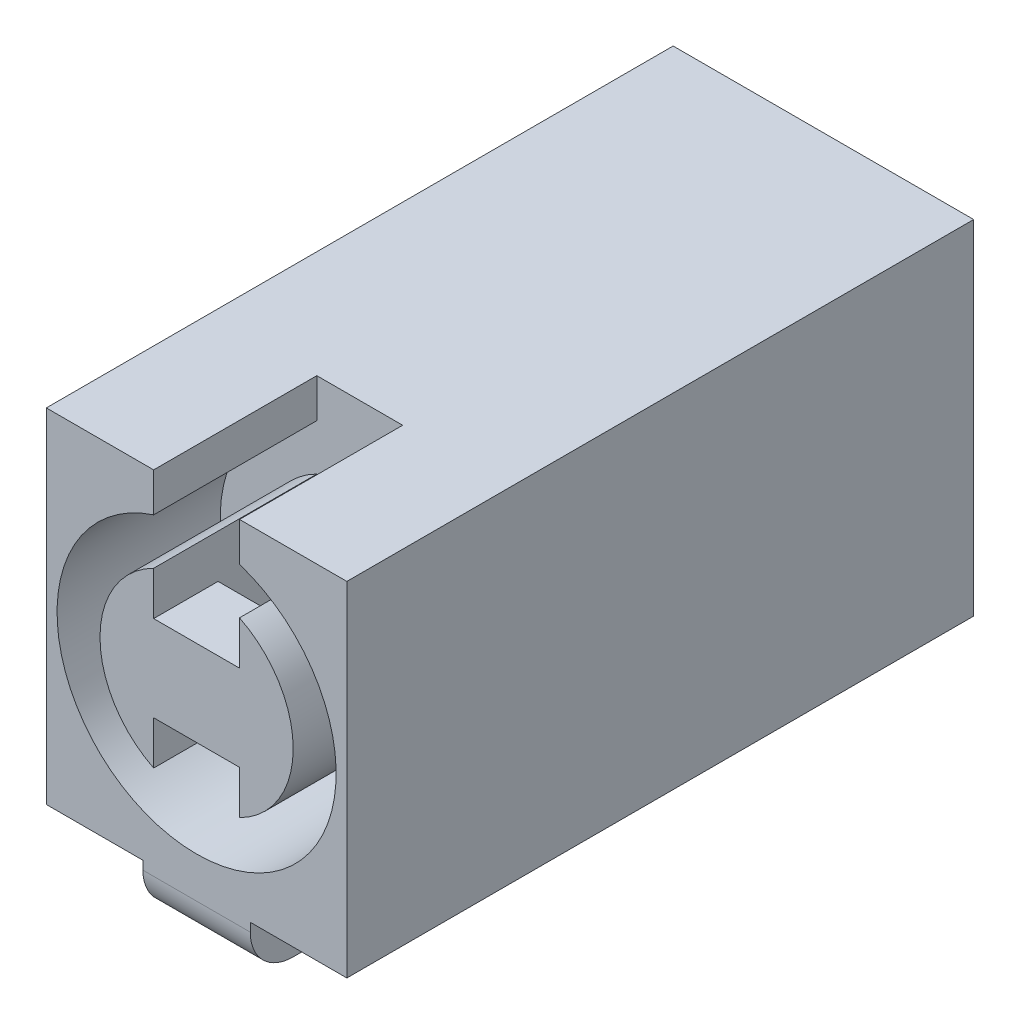
SolidWorks part; units mm, degrees
material "ABS"
ref_plane "Płaszczyzna przednia" through (0, 0, 0) normal (0, 0, 1) x (1, 0, 0)
ref_plane "Płaszczyzna górna" through (0, 0, 0) normal (0, 1, 0) x (1, 0, 0)
ref_plane "Płaszczyzna prawa" through (0, 0, 0) normal (1, 0, 0) x (0, 0, -1)
sketch "Szkic1" plane through (0, 0, 0) normal (0, 1, 0) x (1, 0, 0)
  line L1 (0, 0) -> (7, 0)
  line L2 (0, 0) -> (0, 14.6)
  line L3 (0, 14.6) -> (7, 14.6)
  line L4 (7, 0) -> (7, 14.6)
  dimension "D1" = 7
  dimension "D2" = 14.6
extrude "Dodanie-wyciągnięcie1" add sketch "Szkic1" along normal blind 8
sketch "Szkic2" plane through (0, 0, 0) normal (0, -1, 0) x (1, 0, 0)
  line L0 (7, 0) -> (7, -14.6) construction
  line L1 (2.5, -9.8) -> (4.5, -9.8)
  line L2 (2.5, -9.8) -> (2.5, -4.8)
  line L3 (2.5, -4.8) -> (4.5, -4.8)
  line L4 (4.5, -9.8) -> (4.5, -4.8)
  line L5 (0, 0) -> (7, 0) construction
  point P6 (7, -7.3)
  point P7 (4.5, -7.3)
  point P10 (3.5, 0)
  point P11 (3.5, -4.8)
  dimension "D1" = 5
  dimension "D2" = 2
extrude "Wytnij-wyciągnięcie1" cut sketch "Szkic2" against normal blind 3.5
sketch "Szkic7" plane through (0, 0, 0) normal (0, 0, 1) x (1, 0, 0)
  line L0 (0, 8) -> (7, 8) construction
  line L3 (0, 8) -> (0, 0) construction
  circle A0 centre (3.5, 4) radius 3.25
  circle A1 centre (3.5, 4) radius 2.25
  point P5 (3.5, 8)
  point P7 (0, 4)
  dimension "D1" = 1
  dimension "D2" = 6.5
extrude "Wytnij-wyciągnięcie4" cut sketch "Szkic7" against normal blind 3.8 contours A0 A1
sketch "Szkic10" plane through (0, 0, 0) normal (0, 0, 1) x (1, 0, 0)
  line L0 (0, 8) -> (7, 8) construction
  line L19 (4.5, 7.0923) -> (2.5, 7.0923)
  line L20 (4.5, 7.0923) -> (4.5, 0.9077)
  line L21 (4.5, 0.9077) -> (2.5, 0.9077)
  line L22 (2.5, 7.0923) -> (2.5, 0.9077)
  circle A2 centre (3.5, 4) radius 3.25 construction
  point P6 (3.5, 8)
  point P13 (3.5, 7.0923)
  dimension "D1" = 2
extrude "Wytnij-wyciągnięcie6" cut sketch "Szkic10" against normal blind 3.8
sketch "Szkic12" plane through (2.5, 0, 0) normal (1, 0, 0) x (0, 0, -1)
  line L0 (0, 1.9844) -> (0, 6.0156) construction
  line L1 (0, 5) -> (1.5, 5)
  line L2 (0, 5) -> (0, 3)
  line L3 (0, 3) -> (1.5, 3)
  line L4 (1.5, 5) -> (1.5, 3)
  point P6 (0, 4)
  point P7 (0, 4)
  dimension "D1" = 2
  dimension "D2" = 1.5
extrude "Dodanie-wyciągnięcie4" add sketch "Szkic12" along normal blind 2
sketch "Szkic15" plane through (0, 0, 0) normal (0, -1, 0) x (1, 0, 0)
  line L0 (0, 0) -> (7, 0) construction
  line L12 (2.25, -4.8) -> (4.75, -4.8)
  line L13 (2.25, -4.8) -> (2.25, 0)
  line L14 (2.25, 0) -> (4.75, 0)
  line L15 (4.75, -4.8) -> (4.75, 0)
  line L17 (4.5, -4.8) -> (2.5, -4.8) construction
  line L18 (0, -7.3) -> (7, -7.3) construction
  line L19 (0, -14.6) -> (0, 0) construction
  line L20 (7, 0) -> (7, -14.6) construction
  line L21 (2.25, -14.6) -> (4.75, -14.6)
  line L22 (4.75, -9.8) -> (4.75, -14.6)
  line L23 (2.25, -9.8) -> (4.75, -9.8)
  line L24 (2.25, -9.8) -> (2.25, -14.6)
  point P7 (3.5, -4.8)
  point P9 (3.5, -4.8)
  dimension "D1" = 2.5
extrude "Dodanie-wyciągnięcie6" add sketch "Szkic15" along normal blind 1.2
sketch "Szkic16" plane through (0, 3.5, 0) normal (0, -1, 0) x (1, 0, 0)
  line L0 (2.5, -4.8) -> (2.5, -9.8) construction
  line L1 (2.5, -7.8) -> (4.5, -7.8)
  line L2 (2.5, -7.8) -> (2.5, -6.8)
  line L3 (2.5, -6.8) -> (4.5, -6.8)
  line L4 (4.5, -7.8) -> (4.5, -6.8)
  line L5 (4.5, -9.8) -> (4.5, -4.8) construction
  point P8 (4.5, -7.3)
  point P9 (4.5, -7.3)
  dimension "D1" = 1
extrude "Dodanie-wyciągnięcie7" add sketch "Szkic16" along normal blind 1
fillet "Zaokrąglenie2" radius 1 2 edges at (3.5, -1.2, -14.6) (3.5, -1.2, 0)
sketch "Szkic17" plane through (0, 8, 0) normal (0, 1, 0) x (1, 0, 0)
  line L0 (0, 0) -> (7, 0) construction
  line L1 (2.5, 0) -> (4.5, 0)
  line L2 (2.5, 0) -> (2.5, 3.8)
  line L3 (2.5, 3.8) -> (4.5, 3.8)
  line L4 (4.5, 0) -> (4.5, 3.8)
  point P6 (3.5, 0)
  point P7 (3.5, 0)
  dimension "D1" = 2
  dimension "D2" = 3.8
extrude "Wytnij-wyciągnięcie7" cut sketch "Szkic17" against normal blind 2
